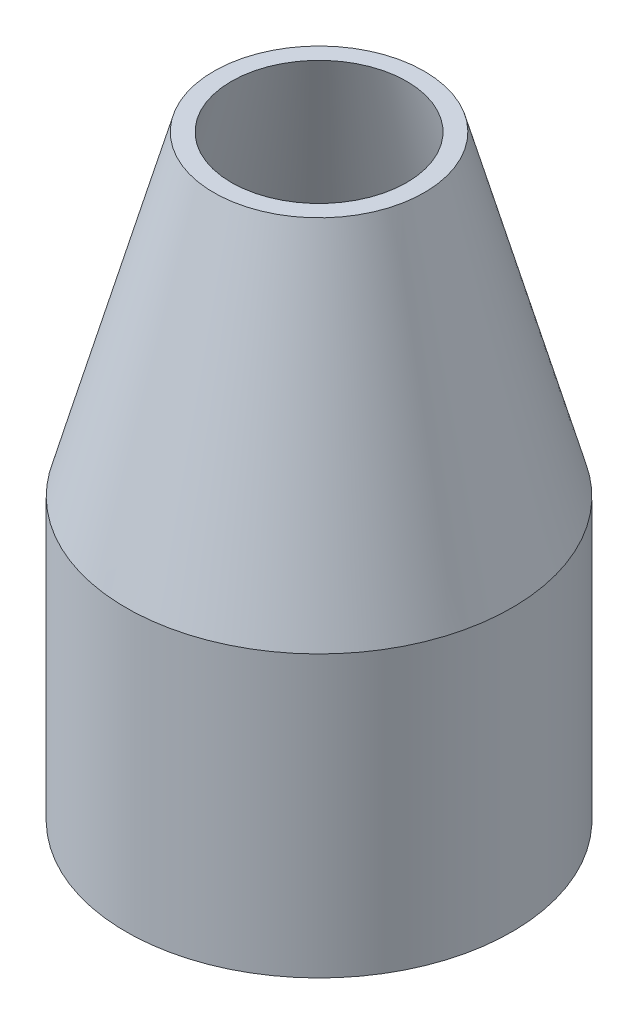
SolidWorks part; units mm, degrees
ref_plane "Front Plane" through (0, 0, 0) normal (0, 0, 1) x (1, 0, 0)
ref_plane "Top Plane" through (0, 0, 0) normal (0, 1, 0) x (1, 0, 0)
ref_plane "Right Plane" through (0, 0, 0) normal (1, 0, 0) x (0, 0, -1)
sketch "Sketch1" plane through (0, 0, 0) normal (0, 0, 1) x (1, 0, 0)
  line L0 (0, 0) -> (0, 60.8172) construction
  line L1 (5.5, 0) -> (5.5, 8)
  line L2 (5.5, 8) -> (3, 17)
  line L3 (3, 17) -> (2.5, 17)
  line L4 (2.5, 17) -> (5, 8)
  line L5 (5, 8) -> (5, 0)
  line L6 (5, 0) -> (5.5, 0)
  dimension "D1" = 0.5
  dimension "D2" = 17
  dimension "D4" = 5
  dimension "D5" = 8
revolve "Revolve2" add sketch "Sketch1" angle 360 about L0
